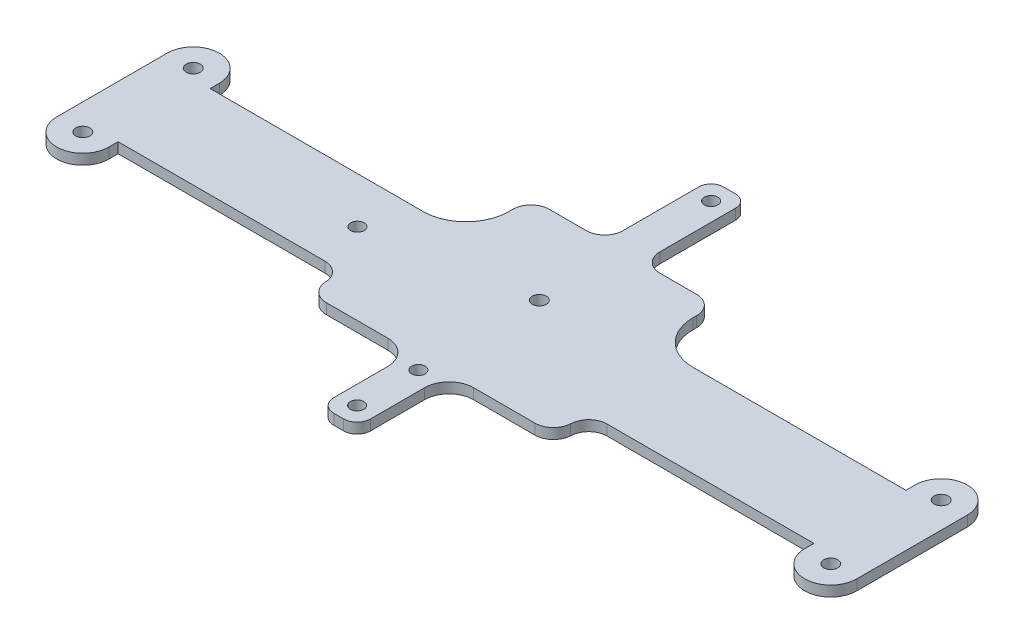
SolidWorks part; units mm, degrees
ref_plane "Płaszczyzna przednia" through (0, 0, 0) normal (0, 0, 1) x (1, 0, 0)
ref_plane "Płaszczyzna górna" through (0, 0, 0) normal (0, 1, 0) x (1, 0, 0)
ref_plane "Płaszczyzna prawa" through (0, 0, 0) normal (1, 0, 0) x (0, 0, -1)
sketch "Szkic1" plane through (0, 7.0875, 0) normal (0, -1, 0) x (1, 0, 0)
  line L0 (-166.869, 45.27) -> (-166.869, 48.27) construction
  line L1 (-166.869, 45.27) -> (-166.869, 48.27)
  line L2 (-44.969, 30.27) -> (-44.969, 31.77) construction
  line L3 (-36.469, 33.27) -> (-36.469, 30.27) construction
  line L4 (-36.469, 48.27) -> (-36.469, 45.27) construction
  line L5 (-44.969, 46.77) -> (-44.969, 48.27) construction
  line L6 (-158.369, 31.77) -> (-158.369, 30.27) construction
  line L7 (-166.869, 30.27) -> (-166.869, 33.27) construction
  line L8 (-158.369, 48.27) -> (-158.369, 46.77) construction
  line L9 (-44.969, 30.27) -> (-44.969, 31.77)
  line L10 (-36.469, 33.27) -> (-36.469, 30.27)
  line L11 (-36.469, 48.27) -> (-36.469, 45.27)
  line L12 (-44.969, 46.77) -> (-44.969, 48.27)
  line L13 (-158.369, 31.77) -> (-158.369, 30.27)
  line L14 (-166.869, 30.27) -> (-166.869, 33.27)
  line L15 (-158.369, 48.27) -> (-158.369, 46.77)
  line L16 (-166.869, 33.27) -> (-166.869, 45.27)
  line L17 (-36.469, 45.27) -> (-36.469, 33.27)
  line L18 (-158.369, 46.77) -> (-124.669, 46.77)
  line L19 (-44.969, 31.77) -> (-79.669, 31.77)
  line L20 (-101.669, 68.1389) -> (-101.669, 67.52) construction
  line L21 (-116.669, 24.77) -> (-116.669, 24.17)
  line L22 (-113.669, 21.17) -> (-107.669, 21.17)
  line L23 (-86.669, 24.17) -> (-86.669, 24.77)
  line L24 (-123.669, 31.77) -> (-158.369, 31.77)
  line L26 (-104.669, 18.17) -> (-104.669, 5.82)
  line L28 (-102.669, 3.82) -> (-100.669, 3.82)
  line L29 (-98.669, 5.82) -> (-98.669, 18.17)
  line L30 (-95.669, 21.17) -> (-89.669, 21.17)
  line L31 (-104.669, 56.52) -> (-104.669, 65.32)
  line L32 (-102.469, 67.52) -> (-100.869, 67.52)
  line L33 (-98.669, 65.32) -> (-98.669, 56.52)
  line L34 (-94.669, 52.52) -> (-84.669, 52.52)
  line L35 (-101.669, 34.82) -> (-101.669, -15.6805) construction
  line L49 (-121.669, 49.77) -> (-121.669, 49.52)
  line L50 (-118.669, 52.52) -> (-108.669, 52.52)
  line L51 (-81.669, 49.52) -> (-81.669, 49.77)
  line L52 (-78.669, 46.77) -> (-44.969, 46.77)
  arc A0 (-44.969, 30.27) -> (-36.469, 30.27) centre (-40.719, 30.27) ccw construction
  arc A1 (-36.469, 48.27) -> (-44.969, 48.27) centre (-40.719, 48.27) ccw construction
  arc A2 (-166.869, 30.27) -> (-158.369, 30.27) centre (-162.619, 30.27) ccw construction
  arc A3 (-158.369, 48.27) -> (-166.869, 48.27) centre (-162.619, 48.27) ccw construction
  arc A4 (-44.969, 30.27) -> (-36.469, 30.27) centre (-40.719, 30.27) ccw
  arc A5 (-36.469, 48.27) -> (-44.969, 48.27) centre (-40.719, 48.27) ccw
  arc A6 (-166.869, 30.27) -> (-158.369, 30.27) centre (-162.619, 30.27) ccw
  arc A7 (-158.369, 48.27) -> (-166.869, 48.27) centre (-162.619, 48.27) ccw
  arc A8 (-86.669, 24.17) -> (-89.669, 21.17) centre (-89.669, 24.17) cw
  arc A9 (-116.669, 24.17) -> (-113.669, 21.17) centre (-113.669, 24.17) ccw
  arc A10 (-79.669, 31.77) -> (-86.669, 24.77) centre (-79.669, 24.77) ccw
  arc A11 (-123.669, 31.77) -> (-116.669, 24.77) centre (-123.669, 24.77) cw
  arc A16 (-163.769, 30.27) -> (-161.469, 30.27) centre (-162.619, 30.27) ccw construction
  arc A17 (-161.469, 48.27) -> (-163.769, 48.27) centre (-162.619, 48.27) ccw construction
  arc A18 (-39.569, 48.27) -> (-41.869, 48.27) centre (-40.719, 48.27) ccw construction
  arc A19 (-41.869, 30.27) -> (-39.569, 30.27) centre (-40.719, 30.27) ccw construction
  circle A24 centre (-162.619, 30.27) radius 1.15
  circle A25 centre (-162.619, 48.27) radius 1.15
  circle A26 centre (-40.719, 48.27) radius 1.15
  circle A27 centre (-40.719, 30.27) radius 1.15
  arc A28 (-81.669, 49.77) -> (-78.669, 46.77) centre (-78.669, 49.77) ccw
  arc A29 (-84.669, 52.52) -> (-81.669, 49.52) centre (-84.669, 49.52) cw
  arc A30 (-121.669, 49.52) -> (-118.669, 52.52) centre (-118.669, 49.52) cw
  arc A31 (-121.669, 49.77) -> (-124.669, 46.77) centre (-124.669, 49.77) cw
  circle A33 centre (-101.669, 6.82) radius 1.1
  arc A34 (-104.669, 5.82) -> (-102.669, 3.82) centre (-102.669, 5.82) ccw
  arc A35 (-100.669, 3.82) -> (-98.669, 5.82) centre (-100.669, 5.82) ccw
  arc A36 (-98.669, 18.17) -> (-95.669, 21.17) centre (-95.669, 18.17) cw
  arc A37 (-104.669, 18.17) -> (-107.669, 21.17) centre (-107.669, 18.17) ccw
  arc A38 (-98.669, 65.32) -> (-100.869, 67.52) centre (-100.869, 65.32) ccw
  arc A39 (-104.669, 65.32) -> (-102.469, 67.52) centre (-102.469, 65.32) cw
  arc A40 (-108.669, 52.52) -> (-104.669, 56.52) centre (-108.669, 56.52) ccw
  arc A41 (-94.669, 52.52) -> (-98.669, 56.52) centre (-94.669, 56.52) cw
  circle A42 centre (-126.869, 39.27) radius 1.1
  circle A43 centre (-101.669, 54.52) radius 1.1
  circle A44 centre (-101.669, 64.52) radius 1.1
  circle A45 centre (-101.669, 34.82) radius 1.15
  point P35 (-116.669, 31.77)
  point P50 (-81.669, 46.77)
  point P60 (-162.619, 52.52)
  point P79 (-98.669, 21.17)
  point P96 (-98.669, 52.52)
  dimension "D4" = 3
  dimension "D5" = 7
  dimension "D6" = 31.35
  dimension "D7" = 20
  dimension "D9" = 3
  dimension "D12" = 28
  dimension "D16" = 2.2
  dimension "D17" = 2
  dimension "D19" = 3
  dimension "D20" = 2.2
  dimension "D22" = 4
  dimension "D23" = 2.2
  dimension "D25" = 2.2
  dimension "D26" = 2.2
  dimension "D13" = 2.3
  dimension "D1" = 15
  dimension "D2" = 15
  dimension "D3" = 25.6
  dimension "D8" = 20
  dimension "D10" = 0
  dimension "D11" = 14.35
  dimension "D14" = 3
  dimension "D15" = 3
  dimension "D18" = 3
  dimension "D21" = 15
  dimension "D24" = 40
  dimension "D27" = 7.5
  dimension "D28" = 3
  dimension "D29" = 3
  dimension "D30" = 10
  dimension "D31" = 3
extrude "Dodanie-wyciągnięcie1" add sketch "Szkic1" along normal blind 1.7
